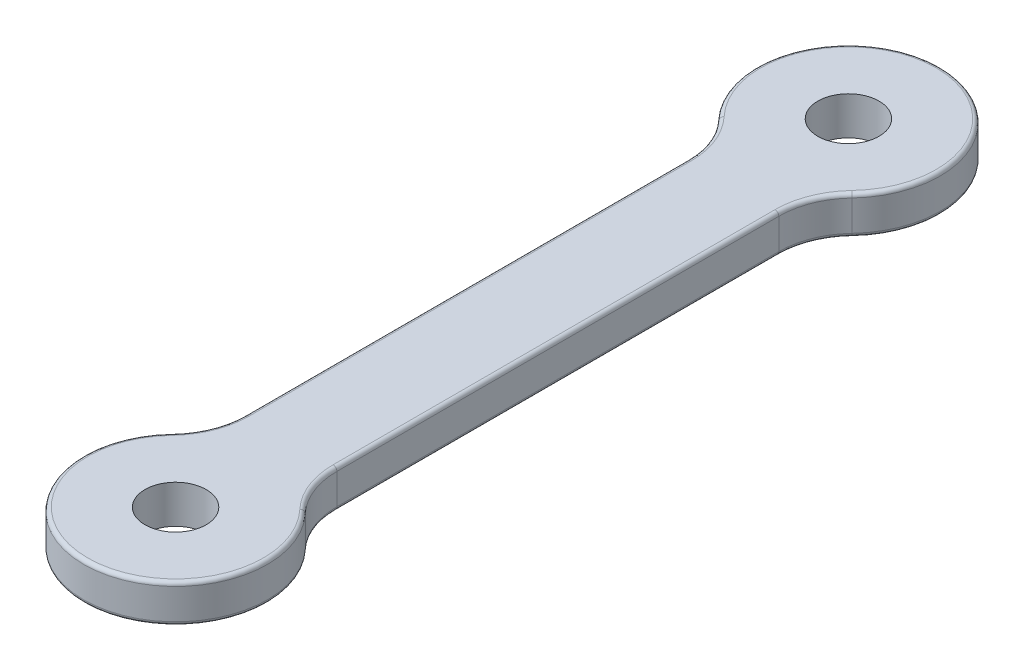
SolidWorks part; units mm, degrees
ref_plane "Front Plane" through (0, 0, 0) normal (0, 0, 1) x (1, 0, 0)
ref_plane "Top Plane" through (0, 0, 0) normal (0, 1, 0) x (1, 0, 0)
ref_plane "Right Plane" through (0, 0, 0) normal (1, 0, 0) x (0, 0, -1)
sketch "Sketch1" plane through (0, 0, 0) normal (0, 1, 0) x (1, 0, 0)
  line L1 (-3, -22) -> (3, -22)
  line L2 (-3, -22) -> (-3, 22)
  line L3 (-3, 22) -> (3, 22)
  line L4 (3, -22) -> (3, 22)
  line L5 (0, 22) -> (0, -22) construction
  line L6 (-3, 0) -> (3, 0) construction
  circle A0 centre (0, 22) radius 6
  circle A1 centre (0, 22) radius 2
  circle A2 centre (0, -22) radius 2
  circle A3 centre (0, -22) radius 6
  point P0 (0, 0)
  dimension "D1" = 4
  dimension "D2" = 12
  dimension "D3" = 44
  dimension "D4" = 6
extrude "Boss-Extrude1" add sketch "Sketch1" along normal blind 2.5 contours A3 L4 A0 L2 | A1 L4 A0 L2 | L2 A3 L4 A2 | L4 A3 L2 A2 | A1 L2 A0 L4
fillet "Fillet1" radius 5 4 edges at (3, 1.25, -16.8038) (3, 1.25, 16.8038) (-3, 1.25, 16.8038) (-3, 1.25, -16.8038)
fillet "Fillet2" radius 0.25 16 edges at (-3.3534, 2.5, 16.2965) (-3.3534, 0, 16.2965) (-3, 0, 0) (-3, 2.5, 0) (-3.3534, 2.5, -16.2965) (-3.3534, 0, -16.2965) (0, 2.5, -28) (0, 0, -28) (3.3534, 2.5, -16.2965) (3.3534, 0, -16.2965) (3, 0, 0) (3, 2.5, 0) (3.3534, 2.5, 16.2965) (3.3534, 0, 16.2965) (0, 0, 28) (0, 2.5, 28)
